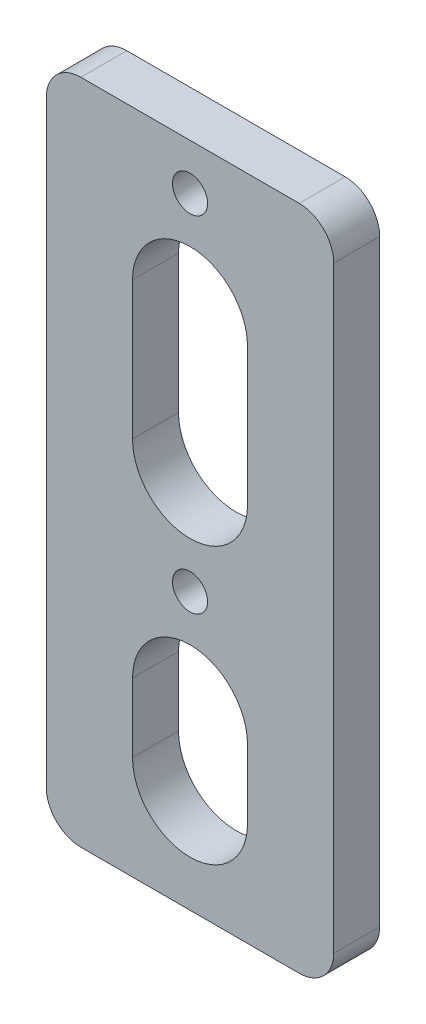
SolidWorks part; units mm, degrees
material "Thornel Mat VMA"
ref_plane "前视基准面" through (0, 0, 0) normal (0, 0, 1) x (1, 0, 0)
ref_plane "上视基准面" through (0, 0, 0) normal (0, 1, 0) x (1, 0, 0)
ref_plane "右视基准面" through (0, 0, 0) normal (1, 0, 0) x (0, 0, -1)
other "Configuration Table"
sketch "草图1" plane through (0, 0, 0) normal (0, 0, 1) x (1, 0, 0)
  line L1 (-12.5, -29) -> (12.5, -29)
  line L2 (-12.5, -29) -> (-12.5, 29)
  line L3 (-12.5, 29) -> (12.5, 29)
  line L4 (12.5, -29) -> (12.5, 29)
  line L5 (-12.5, -29) -> (12.5, 29) construction
  line L6 (-12.5, 29) -> (12.5, -29) construction
  point P0 (0, 0)
  dimension "D1" = 58
  dimension "D2" = 25
extrude "凸台-拉伸1" add sketch "草图1" along normal blind 4
sketch "草图2" plane through (0, 0, 0) normal (0, 0, -1) x (-1, 0, 0)
  circle A0 centre (0, 25) radius 1.525 construction
  circle A1 centre (0, -5) radius 1.525 construction
  circle A2 centre (0, 25) radius 1.525
  circle A3 centre (0, -5) radius 1.525
extrude "切除-拉伸1" cut sketch "草图2" against normal through all both
fillet "圆角1" radius 3 4 edges at (12.5, -29, 2) (-12.5, -29, 2) (12.5, 29, 2) (-12.5, 29, 2)
sketch "草图3" plane through (0, 0, 4) normal (0, 0, 1) x (1, 0, 0)
  line L0 (0, 16) -> (0, 4) construction
  line L1 (5, 16) -> (5, 4)
  line L2 (-5, 16) -> (-5, 4)
  line L3 (0, -14) -> (0, -20) construction
  line L4 (5, -14) -> (5, -20)
  line L5 (-5, -14) -> (-5, -20)
  line L6 (0, 25) -> (0, -5) construction
  line L7 (0, -5) -> (0, -29) construction
  line L8 (-9.5, -29) -> (9.5, -29) construction
  arc A0 (5, 16) -> (-5, 16) centre (0, 16) ccw
  arc A1 (-5, 4) -> (5, 4) centre (0, 4) ccw
  arc A2 (5, -14) -> (-5, -14) centre (0, -14) ccw
  arc A3 (-5, -20) -> (5, -20) centre (0, -20) ccw
  point P3 (0, 10)
  point P8 (0, -17)
  dimension "D2" = 5
  dimension "D3" = 5
  dimension "D1" = 12
  dimension "D4" = 6
extrude "切除-拉伸2" cut sketch "草图3" against normal through all both
